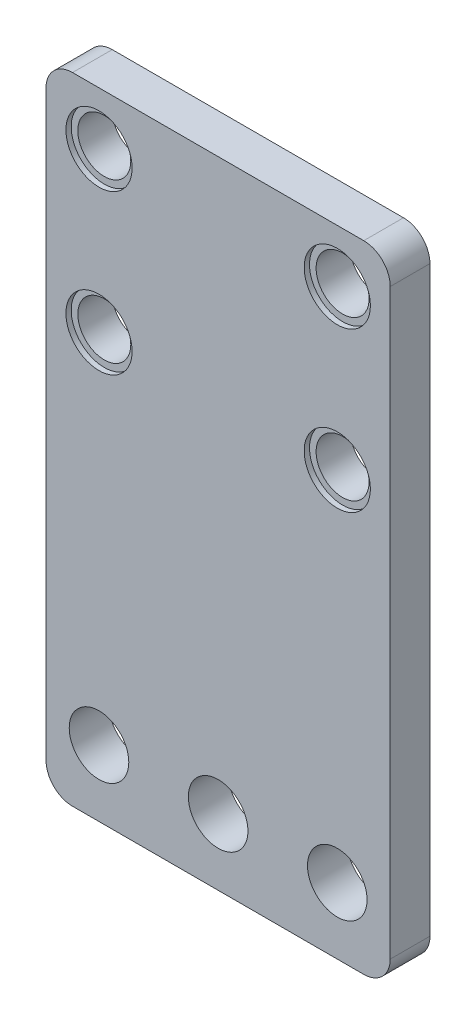
SolidWorks part; units mm, degrees
ref_plane "Plan de face" through (0, 0, 0) normal (0, 0, 1) x (1, 0, 0)
ref_plane "Plan de dessus" through (0, 0, 0) normal (0, 1, 0) x (1, 0, 0)
ref_plane "Plan de droite" through (0, 0, 0) normal (1, 0, 0) x (0, 0, -1)
sketch "Esquisse1" plane through (0, 0, 0) normal (0, 0, 1) x (1, 0, 0)
  line L1 (0, 0) -> (26, 0)
  line L2 (0, 0) -> (0, 48)
  line L3 (0, 48) -> (26, 48)
  line L4 (26, 0) -> (26, 48)
  dimension "D1" = 26
  dimension "D2" = 48
extrude "Boss.-Extru.1" add sketch "Esquisse1" along normal blind 3
sketch "Esquisse2" plane through (0, 0, 3) normal (0, 0, 1) x (1, 0, 0)
  line L0 (13, 0) -> (13, 48) construction
  line L1 (0, 0) -> (26, 0) construction
  line L2 (26, 48) -> (0, 48) construction
  line L3 (13, 38) -> (0, 38) construction
  line L4 (0, 48) -> (0, 0) construction
  circle A0 centre (4, 44) radius 2
  circle A1 centre (4, 32) radius 2
  circle A2 centre (22, 32) radius 2
  circle A3 centre (22, 44) radius 2
  dimension "D1" = 18
  dimension "D2" = 12
  dimension "D3" = 4
  dimension "D4" = 38
extrude "Enlèv. mat.-Extru.1" cut sketch "Esquisse2" against normal through all both and the other way through all
sketch "Esquisse3" plane through (0, 0, 3) normal (0, 0, 1) x (1, 0, 0)
  line L0 (0, 5) -> (26, 5) construction
  line L1 (0, 48) -> (0, 0) construction
  line L2 (26, 0) -> (26, 48) construction
  line L3 (0, 0) -> (26, 0) construction
  line L4 (13, 5) -> (13, 0) construction
  circle A0 centre (13, 5) radius 2.25
  circle A1 centre (4, 5) radius 2.25
  circle A2 centre (22, 5) radius 2.25
  dimension "D2" = 4.5
  dimension "D1" = 5
  dimension "D3" = 18
extrude "Enlèv. mat.-Extru.2" cut sketch "Esquisse3" against normal through all both and the other way through all
sketch "Esquisse4" plane through (0, 0, 3) normal (0, 0, 1) x (1, 0, 0)
  circle A0 centre (4, 32) radius 2.5
  circle A1 centre (22, 32) radius 2.5
  circle A2 centre (22, 44) radius 2.5
  circle A3 centre (4, 44) radius 2.5
  dimension "D1" = 5
extrude "Enlèv. mat.-Extru.3" cut sketch "Esquisse4" against normal blind 0.4
fillet "Congé1" radius 2 4 edges at (0, 48, 1.5) (26, 48, 1.5) (26, 0, 1.5) (0, 0, 1.5)
